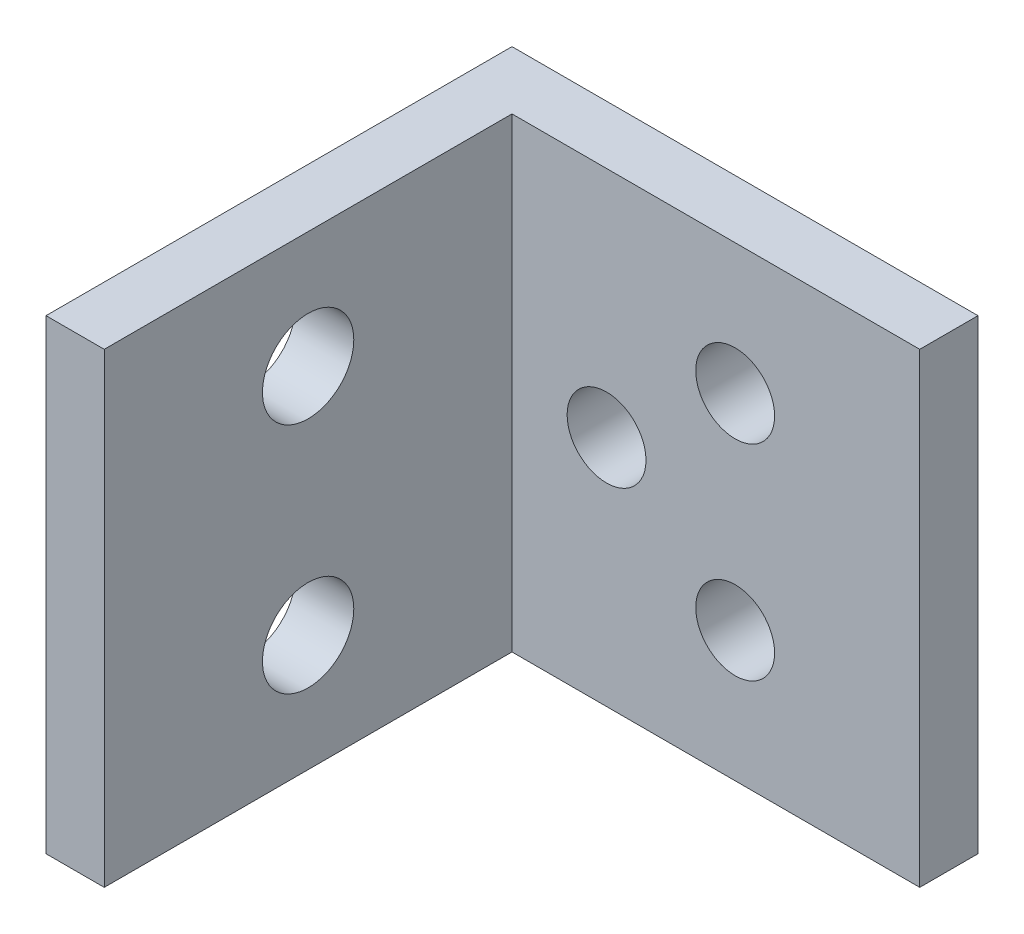
SolidWorks part; units mm, degrees
ref_plane "Front" through (0, 0, 0) normal (0, 0, 1) x (1, 0, 0)
ref_plane "Top" through (0, 0, 0) normal (0, 1, 0) x (1, 0, 0)
ref_plane "Right" through (0, 0, 0) normal (1, 0, 0) x (0, 0, -1)
sketch "Sketch1" plane through (0, 0, 0) normal (0, 1, 0) x (1, 0, 0)
  line L0 (0, 0) -> (25.4, 0)
  line L1 (0, 0) -> (0, -25.4)
  dimension "D1" = 25.4
extrude "Extrude-Thin1" add sketch "Sketch1" along normal blind 25.4 thin
sketch "Sketch3" plane through (0, 0, 0) normal (0, 0, -1) x (-1, 0, 0)
  line L0 (-1.905, 12.7) -> (-23.495, 12.7) construction
  line L1 (-1.905, 28.2956) -> (-1.905, -2.8956)
  line L2 (-1.905, 28.2956) -> (-23.495, 28.2956)
  line L3 (-23.495, 28.2956) -> (-23.495, -2.8956)
  line L4 (-1.905, -2.8956) -> (-23.495, -2.8956)
  line L5 (-1.905, 28.2956) -> (-23.495, -2.8956) construction
  line L6 (-23.495, 28.2956) -> (-1.905, -2.8956) construction
  line L7 (-15.3391, 18.2905) -> (-15.3391, 7.1095) construction
  line L8 (-8.7782, 21.9291) -> (-8.7782, 3.4709) construction
  line L12 (0, 0) -> (-25.4, 25.4) construction
  line L13 (-25.4, 0) -> (0, 25.4) construction
  line L14 (-25.4, 25.4) -> (-25.4, 0) construction
  line L15 (-25.4, 0) -> (0, 0) construction
  line L16 (0, 25.4) -> (0, 0) construction
  circle A0 centre (-8.3287, 12.7) radius 2.1488
  circle A1 centre (-15.3391, 7.1095) radius 2.1488
  circle A2 centre (-15.3391, 18.2905) radius 2.1488
  circle A3 centre (-8.7782, 21.9291) radius 2.1488
  circle A4 centre (-8.7782, 3.4709) radius 2.1488
  point P0 (-12.7, 12.7)
  point P13 (-15.3391, 12.7)
  point P17 (-8.7782, 12.7)
  point P30 (-12.7, 12.7)
  point P31 (-1.905, 28.2812)
  dimension "D6" = 4.2977
  dimension "D1" = 31.1912
  dimension "D2" = 21.59
  dimension "D3" = 8.1559
  dimension "D4" = 11.1811
  dimension "D5" = 6.4237
  dimension "D7" = 18.4582
  dimension "D8" = 6.8732
extrude "Cut-Extrude1" cut sketch "Sketch3" against normal through all contours A0 | A1 | A2
sketch "Sketch4" plane through (3.175, 0, 0) normal (1, 0, 0) x (0, 0, -1)
  line L0 (-14.2875, 0) -> (-14.2875, 25.4) construction
  line L1 (-3.175, 0) -> (-25.4, 0) construction
  line L2 (-3.175, 25.4) -> (-25.4, 25.4) construction
  circle A0 centre (-14.2875, 6.35) radius 2.4892
  circle A1 centre (-14.2875, 19.05) radius 2.4892
  dimension "D1" = 4.9784
  dimension "D2" = 6.35
  dimension "D3" = 12.7
extrude "Cut-Extrude2" cut sketch "Sketch4" against normal through all
